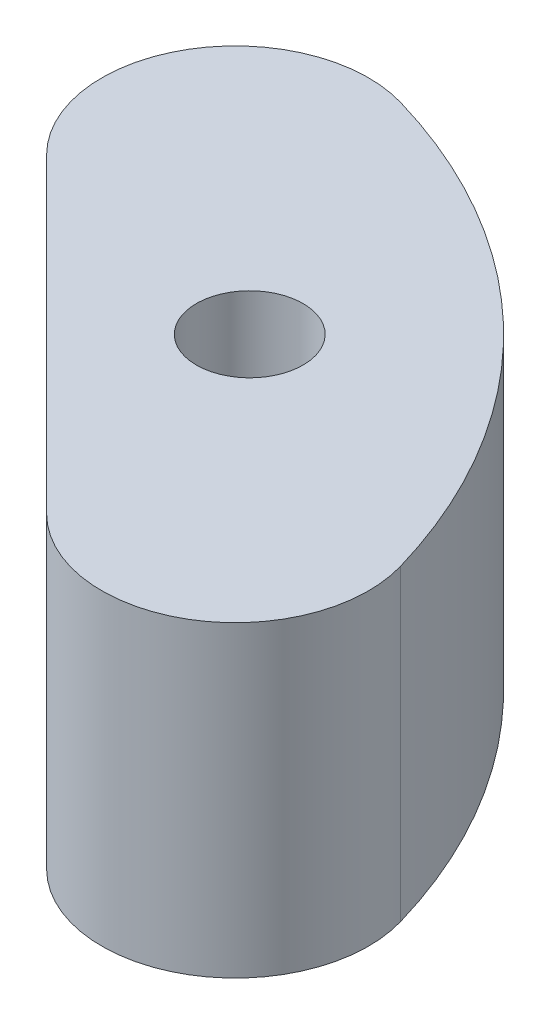
SolidWorks part; units mm, degrees
ref_plane "Front Plane" through (0, 0, 0) normal (0, 0, 1) x (1, 0, 0)
ref_plane "Top Plane" through (0, 0, 0) normal (0, 1, 0) x (1, 0, 0)
ref_plane "Right Plane" through (0, 0, 0) normal (1, 0, 0) x (0, 0, -1)
sketch "Sketch2" plane through (0, 0, 0) normal (0, 1, 0) x (1, 0, 0)
  line L1 (-17.9605, -17.9605) -> (17.9605, -17.9605) construction
  line L2 (-17.9605, -17.9605) -> (-17.9605, 17.9605) construction
  line L3 (-17.9605, 17.9605) -> (17.9605, 17.9605) construction
  line L4 (17.9605, -17.9605) -> (17.9605, 17.9605) construction
  line L5 (-17.9605, -17.9605) -> (17.9605, 17.9605) construction
  line L6 (-17.9605, 17.9605) -> (17.9605, -17.9605) construction
  line L7 (-11.3537, 34.7024) -> (34.7024, -11.3537)
  arc A1 (34.7024, -11.3537) -> (-11.3537, 34.7024) centre (0, 0) ccw
  circle A3 centre (17.9605, 17.9605) radius 3.302
  arc A4 (-11.3537, 34.7024) -> (34.7024, -11.3537) centre (0, 0) ccw construction
  dimension "D1" = 73.025
  dimension "D4" = 6.604
  dimension "D2" = 50.8
  dimension "D3" = 8.89
extrude "Boss-Extrude2" add sketch "Sketch2" along normal mid plane 19.05
sketch "Sketch4" plane through (11.6743, 0, -11.6743) normal (-0.7071, 0, 0.7071) x (0.7071, 0, 0.7071)
  line L1 (-9.97, 6.25) -> (9.97, 6.25) construction
  line L2 (-9.97, 6.25) -> (-9.97, -6.25) construction
  line L3 (-9.97, -6.25) -> (9.97, -6.25) construction
  line L4 (9.97, 6.25) -> (9.97, -6.25) construction
  line L5 (-9.97, 6.25) -> (9.97, -6.25) construction
  line L6 (-9.97, -6.25) -> (9.97, 6.25) construction
  circle A0 centre (9.97, 6.25) radius 1.95
  circle A1 centre (-9.97, 6.25) radius 1.95
  circle A2 centre (-9.97, -6.25) radius 1.95
  circle A3 centre (9.97, -6.25) radius 1.95
  point P0 (0, 0)
  dimension "D1" = 3.9
  dimension "D2" = 19.94
  dimension "D3" = 12.5
extrude "Cut-Extrude2" cut sketch "Sketch4" against normal blind 5.8
fillet "Fillet1" radius 8.255 2 edges at (-11.3537, 0, -34.7024) (34.7024, 0, 11.3537)
equation "\"AIRFRAME_OD\"= 3.091in"
equation "\"AIRFRAME_ID\"= 3.00in"
equation "\"FLAT_T\"= 0.125in"
equation "\"NOSE_EXP_L\"= 3.5in"
equation "\"NOSE_SHOULDER_L\"= 5in"
equation "\"MAIN_L\"= 30in"
equation "\"RECO_COUP_L\"= 6in"
equation "\"RECO_SWITCH_L\"= 1.5in"
equation "\"DROGUE_L\"= 14in"
equation "\"ATS_FORE_COUP_L\"= 4in"
equation "\"ATS_AFT_COUP_L\"= 2.5in"
equation "\"LOWER_L\"= 16in"
equation "\"FIN_N\"= 4"
equation "\"CR_AFT_X\"= 0.5in"
equation "\"CR_FORE_X\"= 6in"
equation "\"COUPLER_OD\"= 2.998in"
equation "\"COUPLER_ID\"= 2.875in"
equation "\"RECO_ROD_X\"= 1.5in"
equation "\"ATS_ROD_X\"= 2in"
equation "\"FIN_ROOT\"= 5in"
equation "\"FIN_X\"= 0.75in"
equation "\"MOTOR_OD\"= 2.25in"
equation "\"MOTOR_ID\"= 2.126in"
equation "\"MOTOR_L\"= 8in"
equation "\"MOTOR_LOWER_X\"= 0.5in"
equation "\"NOSE_CONE_L\"=14.5in"
equation "\"ATS_LIPO_L\"= 1.92in"
equation "\"ATS_LIPO_W\"= 0.42in"
equation "\"ATS_LIPO_H\"= 0.94in "
equation "\"ATS_STANDOFF_H\"= 10mm"
equation "\"ATS_STANDOFF_OD\"= 5.2mm"
equation "\"ATS_PCB_L\"= 2.5in"
equation "\"ATS_PCB_W\"= 1.45in"
equation "\"ATS_PCB_H\"= 1.2in"
equation "\"ATS_PCB_HOLESEP_W\"= 1.33in - 0.0985in"
equation "\"ATS_ALTI_L\"= 1.05in"
equation "\"ATS_ALTI_W\"= 0.7in"
equation "\"ATS_ALTI_H\"= 0.4in"
equation "\"D1@Sketch2\"=\"COUPLER_ID\""
